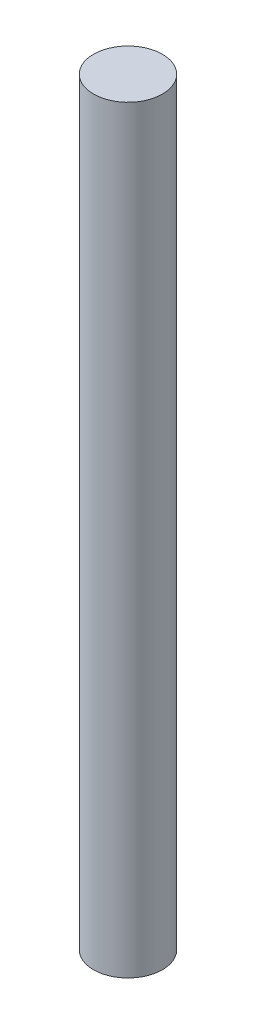
SolidWorks part; units mm, degrees
ref_plane "Front Plane" through (0, 0, 0) normal (0, 0, 1) x (1, 0, 0)
ref_plane "Top Plane" through (0, 0, 0) normal (0, 1, 0) x (1, 0, 0)
ref_plane "Right Plane" through (0, 0, 0) normal (1, 0, 0) x (0, 0, -1)
sketch "Sketch1" plane through (0, 0, 0) normal (0, 1, 0) x (1, 0, 0)
  circle A0 centre (0, 0) radius 12.7
  dimension "D1" = 25.4
extrude "Boss-Extrude1" add sketch "Sketch1" along normal mid plane 279.4 contours A0
